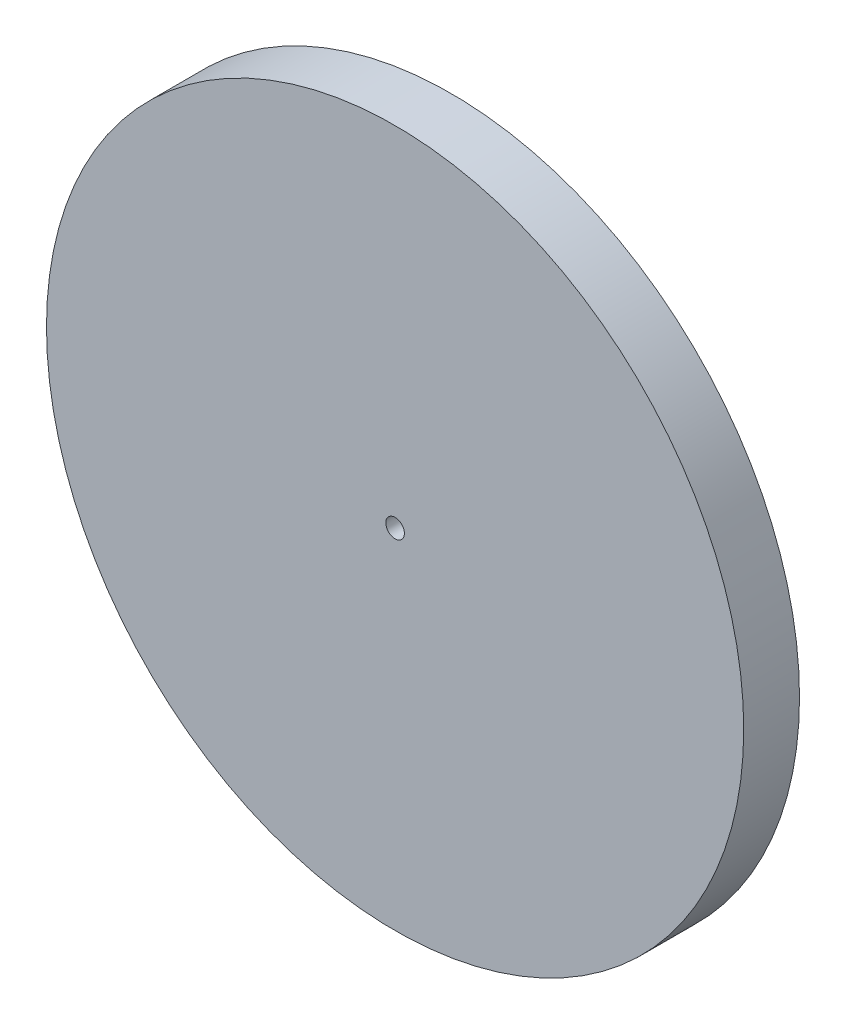
SolidWorks part; units mm, degrees
ref_plane "Front Plane" through (0, 0, 0) normal (0, 0, 1) x (1, 0, 0)
ref_plane "Top Plane" through (0, 0, 0) normal (0, 1, 0) x (1, 0, 0)
ref_plane "Right Plane" through (0, 0, 0) normal (1, 0, 0) x (0, 0, -1)
sketch "Sketch1" plane through (0, 0, 0) normal (0, 0, 1) x (1, 0, 0)
  circle A0 centre (0, 0) radius 37.5
  circle A1 centre (0, 0) radius 1
  dimension "D1" = 2
  dimension "D2" = 75
extrude "Boss-Extrude1" add sketch "Sketch1" along normal blind 6
